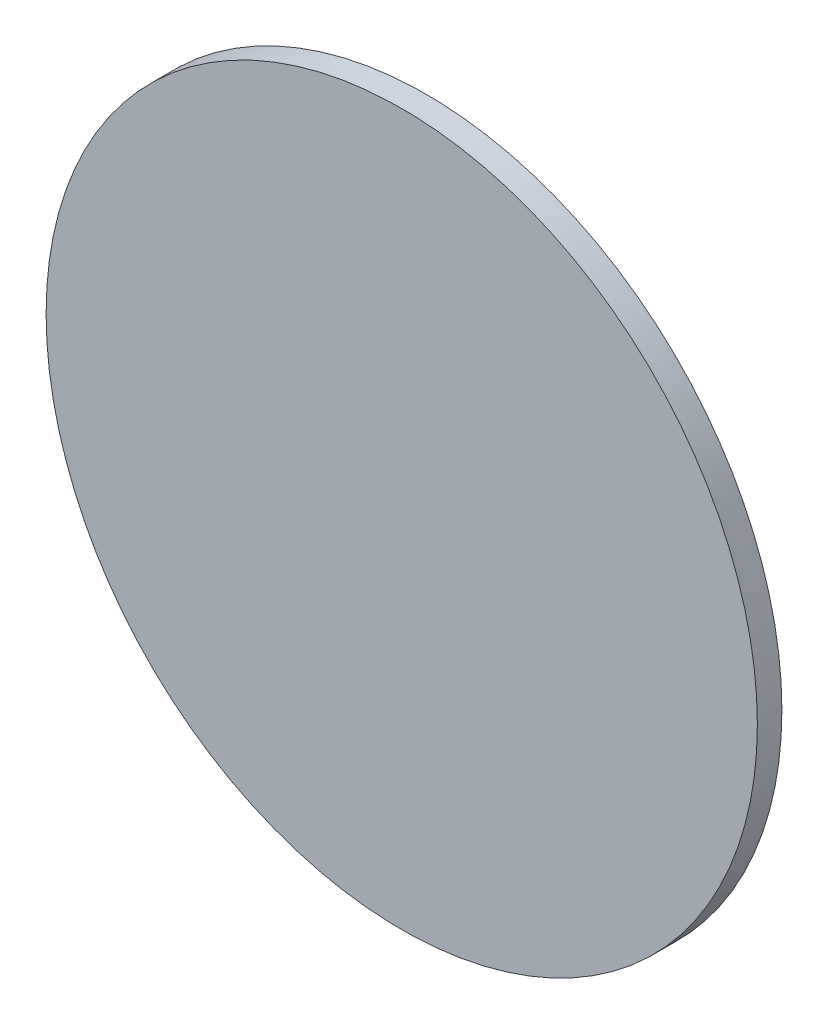
SolidWorks part; units mm, degrees
ref_plane "正面" through (0, 0, 0) normal (0, 0, 1) x (1, 0, 0)
ref_plane "平面" through (0, 0, 0) normal (0, 1, 0) x (1, 0, 0)
ref_plane "右側面" through (0, 0, 0) normal (1, 0, 0) x (0, 0, -1)
sketch "ｽｹｯﾁ1" plane through (0, 0, 0) normal (0, 0, 1) x (1, 0, 0)
  circle A0 centre (0, 0) radius 14.5
  dimension "D1" = 29
extrude "ﾎﾞｽ - 押し出し2" add sketch "ｽｹｯﾁ1" along normal blind 1
sketch "ｽｹｯﾁ2" plane through (0, 0, 1) normal (0, 0, 1) x (1, 0, 0)
  circle A0 centre (-8.25, 0) radius 4.25
  circle A1 centre (8.25, 0) radius 4.25
  circle A2 centre (-8.25, 0) radius 2
  circle A3 centre (8.25, 0) radius 2
  point P8 (-8.25, 0)
  point P9 (8.25, 0)
  dimension "D1" = 8.5
  dimension "D2" = 8.5
  dimension "D5" = 4
  dimension "D6" = 4
  dimension "D3" = 16.5
  dimension "D4" = 8.25
